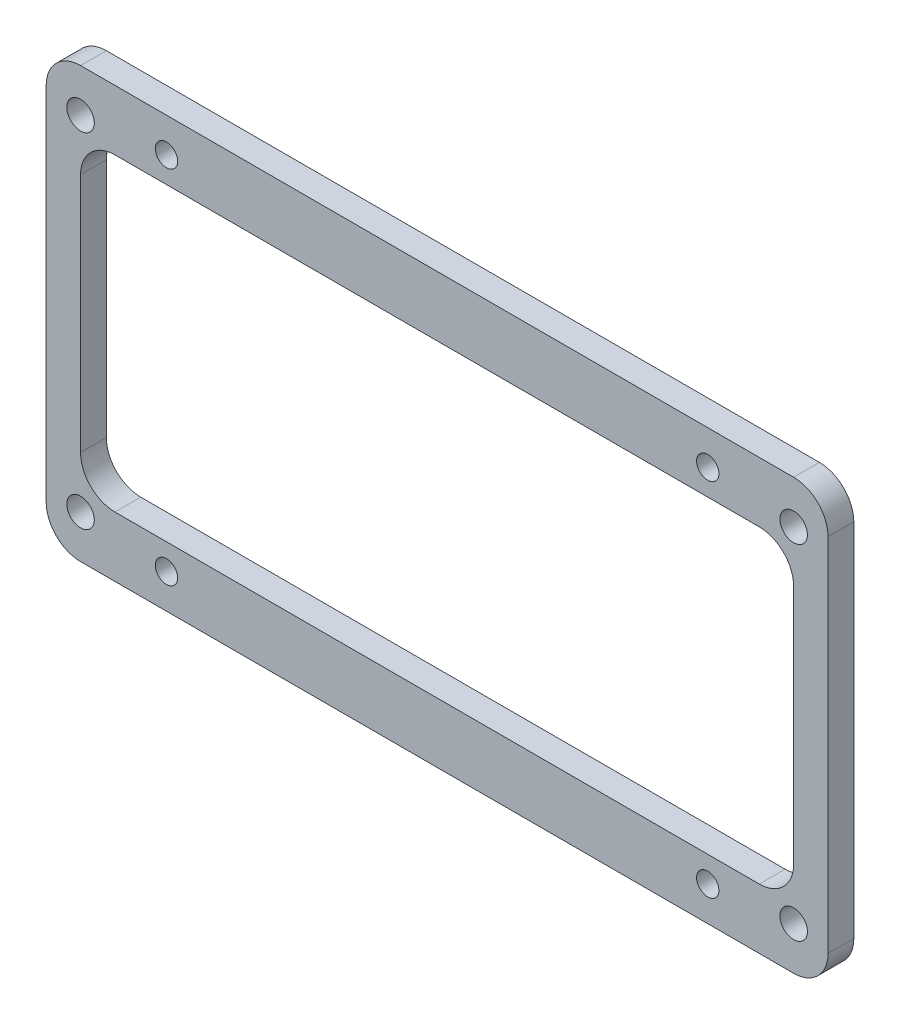
SolidWorks part; units mm, degrees
material "A-玻璃纤维"
ref_plane "前视基准面" through (0, 0, 0) normal (0, 0, 1) x (1, 0, 0)
ref_plane "上视基准面" through (0, 0, 0) normal (0, 1, 0) x (1, 0, 0)
ref_plane "右视基准面" through (0, 0, 0) normal (1, 0, 0) x (0, 0, -1)
sketch "草图1" plane through (0, 0, 0) normal (0, 0, 1) x (1, 0, 0)
  line L1 (-45.5, -25) -> (45.5, -25)
  line L2 (-45.5, -25) -> (-45.5, 25)
  line L3 (-45.5, 25) -> (45.5, 25)
  line L4 (45.5, -25) -> (45.5, 25)
  line L5 (-45.5, -25) -> (45.5, 25) construction
  line L6 (-45.5, 25) -> (45.5, -25) construction
  line L7 (-41.5, -18) -> (41.5, -18)
  line L8 (-41.5, -18) -> (-41.5, 18)
  line L9 (-41.5, 18) -> (41.5, 18)
  line L10 (41.5, -18) -> (41.5, 18)
  line L11 (-41.5, -18) -> (41.5, 18) construction
  line L12 (-41.5, 18) -> (41.5, -18) construction
  point P0 (0, 0)
  point P6 (0, 0)
  dimension "D1" = 50
  dimension "D2" = 91
  dimension "D3" = 36
  dimension "D4" = 83
extrude "凸台-拉伸1" add sketch "草图1" along normal blind 3
sketch "草图2" plane through (0, 0, 3) normal (0, 0, 1) x (1, 0, 0)
  line L1 (-31.5, -21) -> (31.5, -21) construction
  line L2 (-31.5, -21) -> (-31.5, 21) construction
  line L3 (-31.5, 21) -> (31.5, 21) construction
  line L4 (31.5, -21) -> (31.5, 21) construction
  line L5 (-31.5, -21) -> (31.5, 21) construction
  line L6 (-31.5, 21) -> (31.5, -21) construction
  circle A0 centre (31.5, 21) radius 1.3
  circle A1 centre (31.5, -21) radius 1.3
  circle A2 centre (-31.5, -21) radius 1.3
  circle A3 centre (-31.5, 21) radius 1.3
  point P0 (0, 0)
  dimension "D3" = 2.6
  dimension "D1" = 42
  dimension "D2" = 63
extrude "切除-拉伸1" cut sketch "草图2" against normal blind 3
sketch "草图3" plane through (0, 0, 3) normal (0, 0, 1) x (1, 0, 0)
  line L1 (-41.5, -20) -> (41.5, -20) construction
  line L2 (-41.5, -20) -> (-41.5, 20) construction
  line L3 (-41.5, 20) -> (41.5, 20) construction
  line L4 (41.5, -20) -> (41.5, 20) construction
  line L5 (-41.5, -20) -> (41.5, 20) construction
  line L6 (-41.5, 20) -> (41.5, -20) construction
  circle A0 centre (41.5, 20) radius 1.6
  circle A1 centre (41.5, -20) radius 1.6
  circle A2 centre (-41.5, -20) radius 1.6
  circle A3 centre (-41.5, 20) radius 1.6
  point P0 (0, 0)
  dimension "D3" = 3.2
  dimension "D1" = 83
  dimension "D2" = 40
extrude "切除-拉伸2" cut sketch "草图3" against normal blind 3
fillet "圆角1" radius 4 8 edges at (-41.5, -18, 1.5) (41.5, -18, 1.5) (45.5, -25, 1.5) (-45.5, -25, 1.5) (-45.5, 25, 1.5) (45.5, 25, 1.5) (41.5, 18, 1.5) (-41.5, 18, 1.5)
sketch "草图4" plane through (0, 0, 0) normal (0, 0, -1) x (-1, 0, 0)
  line L0 (-45.5, -21) -> (-45.5, 21) construction
  line L1 (-45.5, 17.5) -> (-75.5, 17.5)
  line L2 (-45.5, 17.5) -> (-45.5, -17.5)
  line L3 (-45.5, -17.5) -> (-75.5, -17.5)
  line L4 (-75.5, 17.5) -> (-75.5, -17.5)
  line L5 (-45.5, 0) -> (0, 0) construction
  dimension "D1" = 35
  dimension "D2" = 30
extrude "凸台-拉伸2" add sketch "草图4" against normal up to surface (3 mm away) up to face at (-39.9, 20, 3)
sketch "草图5" plane through (0, 0, 0) normal (0, 0, -1) x (-1, 0, 0)
  line L0 (-70.5, 17.5) -> (-70.5, -17.5) construction
  line L3 (-70.5, 0) -> (0, 0) construction
  line L4 (-75.5, 17.5) -> (-75.5, -17.5) construction
  circle A0 centre (-70.5, -12) radius 1.25
  circle A1 centre (-70.5, 12) radius 1.25
  dimension "D2" = 2.5
  dimension "D1" = 12
  dimension "D3" = 5
extrude "切除-拉伸3" cut sketch "草图5" against normal blind 10
fillet "圆角2" radius 3 4 edges at (45.5, 17.5, 1.5) (75.5, 17.5, 1.5) (75.5, -17.5, 1.5) (45.5, -17.5, 1.5)
sketch "草图6" plane through (0, 0, 0) normal (0, 0, -1) x (-1, 0, 0)
  line L0 (-48.5, 17.5) -> (-72.5, 17.5) construction
  line L5 (-66.5, 13.5) -> (-48.5, 13.5)
  line L6 (-66.5, 13.5) -> (-66.5, -13.5)
  line L7 (-66.5, -13.5) -> (-48.5, -13.5)
  line L8 (-48.5, 13.5) -> (-48.5, -13.5)
  line L9 (-72.5, -17.5) -> (-48.5, -17.5) construction
  circle A0 centre (-70.5, -12) radius 1.25 construction
  dimension "D1" = 4
  dimension "D2" = 4
  dimension "D3" = 4
  dimension "D4" = 3
extrude "切除-拉伸4" cut sketch "草图6" against normal blind 10
fillet "圆角3" radius 2 4 edges at (48.5, 13.5, 1.5) (48.5, -13.5, 1.5) (66.5, -13.5, 1.5) (66.5, 13.5, 1.5)
sketch "草图7" plane through (0, 0, 0) normal (0, 0, -1) x (-1, 0, 0)
  line L0 (-19, 25) -> (19, 25)
  line L1 (-16, -32) -> (16, -32) construction
  line L2 (-16, -32) -> (-16, 32) construction
  line L3 (-16, 32) -> (16, 32) construction
  line L4 (16, -32) -> (16, 32) construction
  line L5 (0, 32) -> (0, -32) construction
  line L6 (-16, 0) -> (16, 0) construction
  line L7 (-19, -35) -> (19, -35)
  line L8 (-19, -35) -> (-19, -25)
  line L9 (-19, 35) -> (19, 35)
  line L10 (19, -35) -> (19, -25)
  line L11 (0, 35) -> (0, -35) construction
  line L12 (-19, 0) -> (19, 0) construction
  line L13 (-41.5, 25) -> (41.5, 25) construction
  line L14 (-19, -25) -> (19, -25)
  line L15 (41.5, -25) -> (-41.5, -25) construction
  line L16 (19, 25) -> (19, 35)
  line L17 (-19, 25) -> (-19, 35)
  circle A0 centre (16, -32) radius 1.6
  circle A1 centre (-16, -32) radius 1.6
  circle A2 centre (-16, 32) radius 1.6
  circle A3 centre (16, 32) radius 1.6
  point P0 (0, 0)
  point P4 (0, 0)
  dimension "D6" = 3.2
  dimension "D1" = 64
  dimension "D2" = 32
  dimension "D3" = 38
  dimension "D4" = 3
  dimension "D5" = 3
extrude "凸台-拉伸3" add sketch "草图7" against normal up to surface (3 mm away) up to face at (57.5, 0, 3)
fillet "圆角4" radius 2 4 edges at (-19, -35, 1.5) (19, -35, 1.5) (-19, 35, 1.5) (19, 35, 1.5)
fillet "圆角5" radius 2 4 edges at (-19, -25, 1.5) (19, -25, 1.5) (19, 25, 1.5) (-19, 25, 1.5)
sketch "草图8" plane through (0, 0, 3) normal (0, 0, 1) x (1, 0, 0)
  line L0 (17, 35) -> (-17, 35) construction
  line L1 (-21, 25) -> (21, 25)
  line L2 (-21, 25) -> (-21, 35)
  line L3 (-21, 35) -> (21, 35)
  line L4 (21, 25) -> (21, 35)
  line L5 (-17, -35) -> (17, -35) construction
  line L6 (-21, -25) -> (21, -25)
  line L7 (-21, -25) -> (-21, -35)
  line L8 (-21, -35) -> (21, -35)
  line L9 (21, -25) -> (21, -35)
extrude "切除-拉伸5" cut sketch "草图8" against normal blind 10
sketch "草图9" plane through (0, 0, 3) normal (0, 0, 1) x (1, 0, 0)
  line L0 (75.5, -14.5) -> (75.5, 14.5) construction
  line L1 (45.5, 20.5) -> (75.5, 20.5)
  line L2 (45.5, 20.5) -> (45.5, -20.5)
  line L3 (45.5, -20.5) -> (75.5, -20.5)
  line L4 (75.5, 20.5) -> (75.5, -20.5)
  point P5 (45.5, -20.5)
extrude "切除-拉伸6" cut sketch "草图9" against normal blind 10
